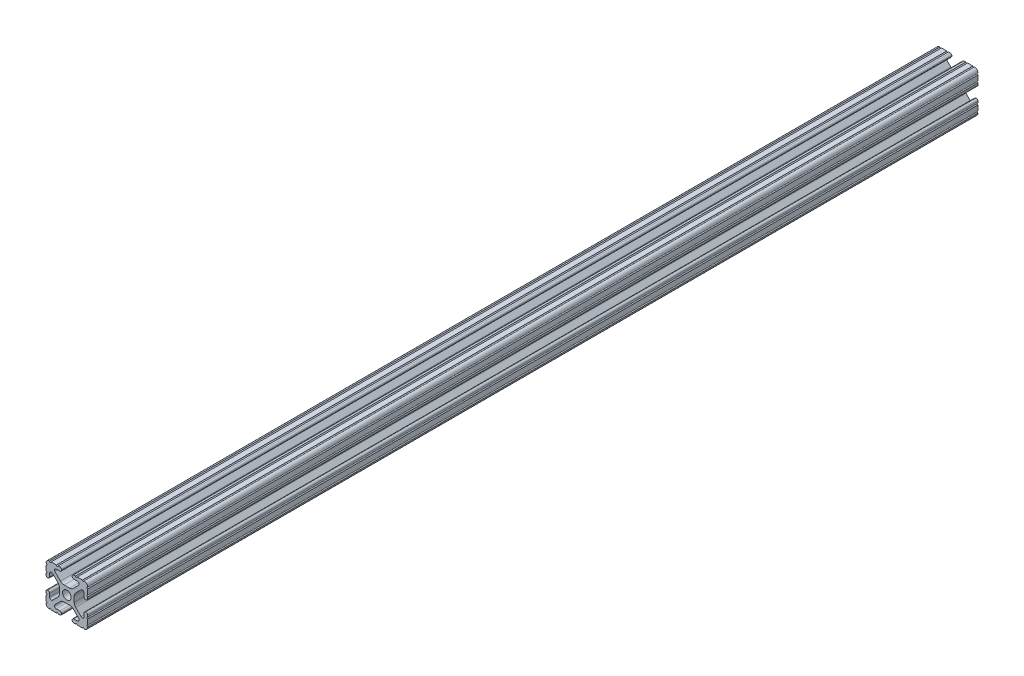
SolidWorks part; units mm, degrees
material "6105-T5 Aluminum"
ref_plane "Front Plane" through (0, 0, 0) normal (0, 0, 1) x (1, 0, 0)
ref_plane "Top Plane" through (0, 0, 0) normal (0, 1, 0) x (1, 0, 0)
ref_plane "Right Plane" through (0, 0, 0) normal (1, 0, 0) x (0, 0, -1)
sketch "Sketch1" plane through (0, 0, 0) normal (0, 0, 1) x (1, 0, 0)
  line L0 (-7.207, 8.7244) -> (-3.8983, 5.4232)
  line L1 (-4.2875, 10.4902) -> (-6.4768, 10.4902)
  line L2 (-3.2385, 11.651) -> (-3.2385, 11.5392)
  line L3 (-5.3171, 12.7) -> (-4.2875, 12.7)
  line L4 (0, 13.4005) -> (0, -14.8534) construction
  line L5 (12.7, 0) -> (-13.9989, 0) construction
  line L6 (-9.5504, 12.7) -> (-6.3331, 12.7)
  line L7 (-12.7, 6.3331) -> (-12.7, 9.5504)
  line L8 (-12.7, 4.2875) -> (-12.7, 5.3171)
  line L9 (-11.5392, 3.2385) -> (-11.651, 3.2385)
  line L10 (-10.4902, 6.4021) -> (-10.4902, 4.2875)
  line L11 (-5.441, 3.8408) -> (-8.7371, 7.1294)
  line L12 (-4.5085, -1.5932) -> (-4.5085, 1.5932)
  line L13 (-1.7093, -4.4958) -> (1.7093, -4.4958)
  line L14 (3.9523, -5.4237) -> (7.1797, -8.6452)
  line L15 (6.4164, -10.4902) -> (4.2875, -10.4902)
  line L16 (3.2385, -11.5392) -> (3.2385, -11.651)
  line L17 (4.2875, -12.7) -> (5.3171, -12.7)
  line L18 (6.3331, -12.7) -> (9.5504, -12.7)
  line L19 (12.7, -9.5504) -> (12.7, -6.3331)
  line L20 (12.7, -5.3171) -> (12.7, -4.2875)
  line L21 (11.651, -3.2385) -> (11.5392, -3.2385)
  line L22 (10.4902, -4.2875) -> (10.4902, -6.4021)
  line L23 (8.7371, -7.1294) -> (5.441, -3.8408)
  line L24 (4.5085, -1.5932) -> (4.5085, 1.5932)
  line L25 (5.441, 3.8408) -> (8.7371, 7.1294)
  line L26 (10.4902, 6.4021) -> (10.4902, 4.2875)
  line L27 (11.5392, 3.2385) -> (11.651, 3.2385)
  line L28 (12.7, 4.2875) -> (12.7, 5.3171)
  line L29 (12.7, 6.3331) -> (12.7, 9.5504)
  line L30 (9.5504, 12.7) -> (6.3331, 12.7)
  line L31 (5.3171, 12.7) -> (4.2875, 12.7)
  line L32 (3.2385, 11.651) -> (3.2385, 11.5392)
  line L33 (4.2875, 10.4902) -> (6.4768, 10.4902)
  line L34 (7.207, 8.7244) -> (3.8983, 5.4232)
  line L35 (1.6558, 4.4958) -> (-1.6558, 4.4958)
  line L36 (-8.7371, -7.1294) -> (-5.441, -3.8408)
  line L37 (-10.4902, -4.2875) -> (-10.4902, -6.4021)
  line L38 (-11.651, -3.2385) -> (-11.5392, -3.2385)
  line L39 (-12.7, -5.3171) -> (-12.7, -4.2875)
  line L40 (-12.7, -9.5504) -> (-12.7, -6.3331)
  line L41 (-6.3331, -12.7) -> (-9.5504, -12.7)
  line L42 (-4.2875, -12.7) -> (-5.3171, -12.7)
  line L43 (-3.2385, -11.5392) -> (-3.2385, -11.651)
  line L44 (-6.4164, -10.4902) -> (-4.2875, -10.4902)
  line L45 (-3.9523, -5.4237) -> (-7.1797, -8.6452)
  arc A0 (-7.207, 8.7244) -> (-6.4768, 10.4902) centre (-6.4768, 9.4563) cw
  arc A1 (-3.2385, 11.5392) -> (-4.2875, 10.4902) centre (-4.2875, 11.5392) cw
  arc A2 (-4.2875, 12.7) -> (-3.2385, 11.651) centre (-4.2875, 11.651) cw
  arc A3 (-5.3171, 12.7) -> (-6.3331, 12.7) centre (-5.8251, 12.7) cw
  arc A4 (-9.5504, 12.7) -> (-10.5664, 12.6998) centre (-10.0584, 12.7) cw
  arc A5 (-12.6998, 10.5664) -> (-10.5664, 12.6998) centre (-10.5918, 10.5918) cw
  arc A6 (-12.6998, 10.5664) -> (-12.7, 9.5504) centre (-12.7, 10.0584) cw
  arc A7 (-12.7, 6.3331) -> (-12.7, 5.3171) centre (-12.7, 5.8251) cw
  arc A8 (-11.651, 3.2385) -> (-12.7, 4.2875) centre (-11.651, 4.2875) cw
  arc A9 (-10.4902, 4.2875) -> (-11.5392, 3.2385) centre (-11.5392, 4.2875) cw
  circle A10 centre (0, 0) radius 2.6035
  arc A11 (-10.4902, 6.4021) -> (-8.7371, 7.1294) centre (-9.4628, 6.4021) cw
  arc A12 (-5.441, 3.8408) -> (-4.5085, 1.5932) centre (-7.6835, 1.5932) cw
  arc A13 (-4.5085, -1.5932) -> (-5.441, -3.8408) centre (-7.6835, -1.5932) cw
  arc A14 (-8.7371, -7.1294) -> (-10.4902, -6.4021) centre (-9.4628, -6.4021) cw
  arc A15 (-1.7093, -4.4958) -> (-3.9523, -5.4237) centre (-1.7093, -7.6708) ccw
  arc A16 (3.9523, -5.4237) -> (1.7093, -4.4958) centre (1.7093, -7.6708) ccw
  arc A17 (6.4164, -10.4902) -> (7.1797, -8.6452) centre (6.4164, -9.4098) ccw
  arc A18 (4.2875, -10.4902) -> (3.2385, -11.5392) centre (4.2875, -11.5392) ccw
  arc A19 (3.2385, -11.651) -> (4.2875, -12.7) centre (4.2875, -11.651) ccw
  arc A20 (6.3331, -12.7) -> (5.3171, -12.7) centre (5.8251, -12.7) ccw
  arc A21 (10.5664, -12.6998) -> (9.5504, -12.7) centre (10.0584, -12.7) ccw
  arc A22 (10.5664, -12.6998) -> (12.6998, -10.5664) centre (10.5918, -10.5918) ccw
  arc A23 (12.7, -9.5504) -> (12.6998, -10.5664) centre (12.7, -10.0584) ccw
  arc A24 (12.7, -5.3171) -> (12.7, -6.3331) centre (12.7, -5.8251) ccw
  arc A25 (12.7, -4.2875) -> (11.651, -3.2385) centre (11.651, -4.2875) ccw
  arc A26 (11.5392, -3.2385) -> (10.4902, -4.2875) centre (11.5392, -4.2875) ccw
  arc A27 (8.7371, -7.1294) -> (10.4902, -6.4021) centre (9.4628, -6.4021) ccw
  arc A28 (4.5085, -1.5932) -> (5.441, -3.8408) centre (7.6835, -1.5932) ccw
  arc A29 (5.441, 3.8408) -> (4.5085, 1.5932) centre (7.6835, 1.5932) ccw
  arc A30 (10.4902, 6.4021) -> (8.7371, 7.1294) centre (9.4628, 6.4021) ccw
  arc A31 (10.4902, 4.2875) -> (11.5392, 3.2385) centre (11.5392, 4.2875) ccw
  arc A32 (11.651, 3.2385) -> (12.7, 4.2875) centre (11.651, 4.2875) ccw
  arc A33 (12.7, 6.3331) -> (12.7, 5.3171) centre (12.7, 5.8251) ccw
  arc A34 (12.6998, 10.5664) -> (12.7, 9.5504) centre (12.7, 10.0584) ccw
  arc A35 (12.6998, 10.5664) -> (10.5664, 12.6998) centre (10.5918, 10.5918) ccw
  arc A36 (9.5504, 12.7) -> (10.5664, 12.6998) centre (10.0584, 12.7) ccw
  arc A37 (5.3171, 12.7) -> (6.3331, 12.7) centre (5.8251, 12.7) ccw
  arc A38 (4.2875, 12.7) -> (3.2385, 11.651) centre (4.2875, 11.651) ccw
  arc A39 (3.2385, 11.5392) -> (4.2875, 10.4902) centre (4.2875, 11.5392) ccw
  arc A40 (7.207, 8.7244) -> (6.4768, 10.4902) centre (6.4768, 9.4563) ccw
  arc A41 (1.6558, 4.4958) -> (3.8983, 5.4232) centre (1.6558, 7.6708) ccw
  arc A42 (-1.6558, 4.4958) -> (-3.8983, 5.4232) centre (-1.6558, 7.6708) cw
  arc A43 (-11.5392, -3.2385) -> (-10.4902, -4.2875) centre (-11.5392, -4.2875) cw
  arc A44 (-12.7, -4.2875) -> (-11.651, -3.2385) centre (-11.651, -4.2875) cw
  arc A45 (-12.7, -5.3171) -> (-12.7, -6.3331) centre (-12.7, -5.8251) cw
  arc A46 (-12.7, -9.5504) -> (-12.6998, -10.5664) centre (-12.7, -10.0584) cw
  arc A47 (-10.5664, -12.6998) -> (-12.6998, -10.5664) centre (-10.5918, -10.5918) cw
  arc A48 (-10.5664, -12.6998) -> (-9.5504, -12.7) centre (-10.0584, -12.7) cw
  arc A49 (-6.3331, -12.7) -> (-5.3171, -12.7) centre (-5.8251, -12.7) cw
  arc A50 (-3.2385, -11.651) -> (-4.2875, -12.7) centre (-4.2875, -11.651) cw
  arc A51 (-4.2875, -10.4902) -> (-3.2385, -11.5392) centre (-4.2875, -11.5392) cw
  arc A52 (-6.4164, -10.4902) -> (-7.1797, -8.6452) centre (-6.4164, -9.4098) cw
  dimension "D1" = 5.207
  dimension "D9" = 14.859
  dimension "D2" = 25.4
  dimension "D3" = 12.7
  dimension "D4" = 6.477
  dimension "D5" = 8.2042
  dimension "D6" = 9.017
  dimension "D8" = 2.2098
  dimension "D10" = 2.2098
extrude "Extrude1" add sketch "Sketch1" against normal blind 542.925
